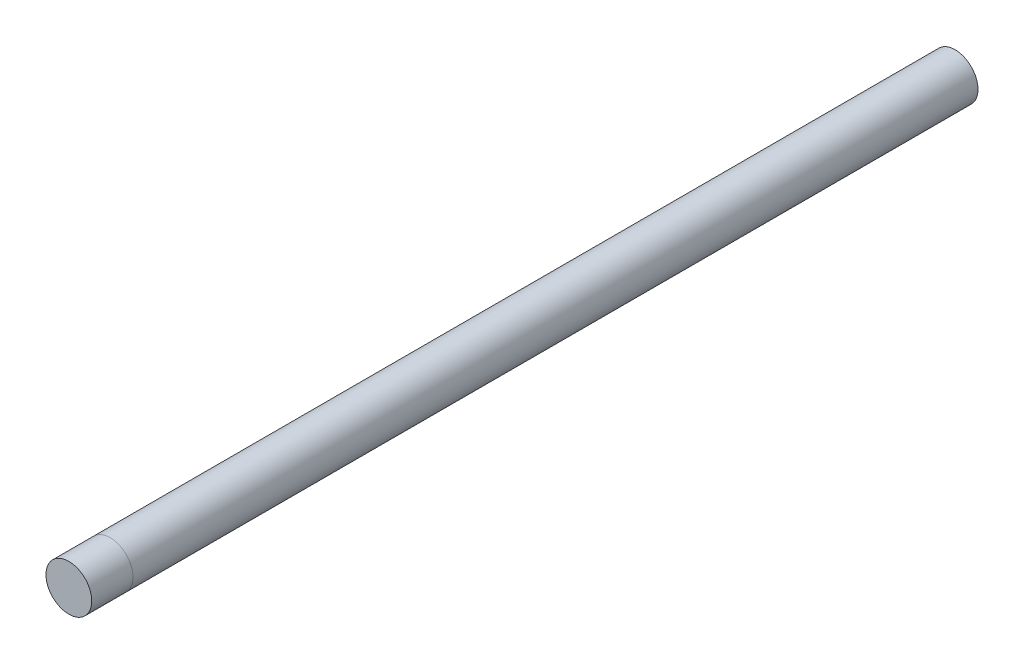
SolidWorks part; units mm, degrees
ref_plane "Front Plane" through (0, 0, 0) normal (0, 0, 1) x (1, 0, 0)
ref_plane "Top Plane" through (0, 0, 0) normal (0, 1, 0) x (1, 0, 0)
ref_plane "Right Plane" through (0, 0, 0) normal (1, 0, 0) x (0, 0, -1)
sketch "Sketch1" plane through (0, 0, 0) normal (0, 0, 1) x (1, 0, 0)
  circle A0 centre (0, 0) radius 5
extrude "Boss-Extrude1" add sketch "Sketch1" along normal blind 184.5
sketch "Sketch2" plane through (0, 0, 184.5) normal (0, 0, 1) x (1, 0, 0)
  circle A0 centre (0, 0) radius 5
extrude "Boss-Extrude2" add sketch "Sketch2" along normal blind 9 separate body
